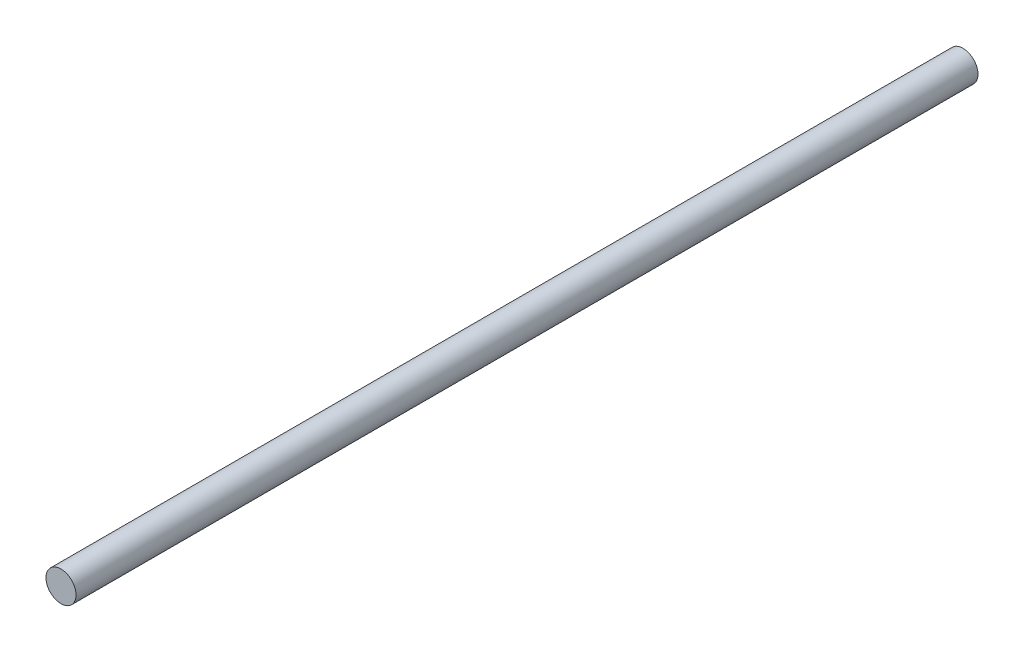
SolidWorks part; units mm, degrees
ref_plane "Front Plane" through (0, 0, 0) normal (0, 0, 1) x (1, 0, 0)
ref_plane "Top Plane" through (0, 0, 0) normal (0, 1, 0) x (1, 0, 0)
ref_plane "Right Plane" through (0, 0, 0) normal (1, 0, 0) x (0, 0, -1)
sketch "Sketch1" plane through (0, 0, 0) normal (0, 0, 1) x (1, 0, 0)
  circle A0 centre (0, 0) radius 10
  dimension "D1" = 10
extrude "Boss-Extrude2" add sketch "Sketch1" along normal blind 600
